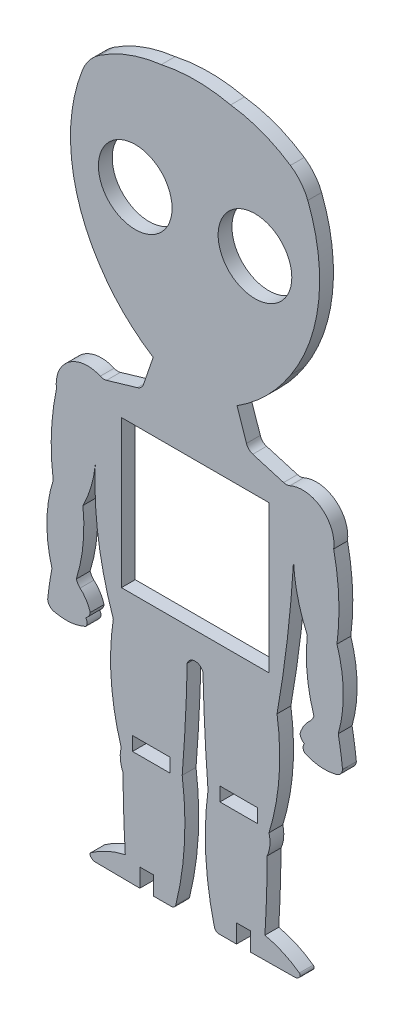
SolidWorks part; units mm, degrees
ref_plane "Alzado" through (0, 0, 0) normal (0, 0, 1) x (1, 0, 0)
ref_plane "Planta" through (0, 0, 0) normal (0, 1, 0) x (1, 0, 0)
ref_plane "Vista lateral" through (0, 0, 0) normal (1, 0, 0) x (0, 0, -1)
sketch "Model" plane through (0, 0, 0) normal (0, 0, 1) x (1, 0, 0)
  line L0 (34.7592, 26.0026) -> (50.2592, 26.0026)
  line L1 (50.2592, 26.0026) -> (50.2592, -5.9974)
  line L2 (50.2592, -5.9974) -> (18.2592, -5.9974)
  line L3 (18.2592, -5.9974) -> (18.2592, 26.0026)
  line L4 (18.2592, 26.0026) -> (33.7592, 26.0026)
  line L5 (33.7592, 26.0026) -> (34.7592, 26.0026)
  line L6 (28.8594, -35.6001) -> (20.6594, -35.6001)
  line L7 (20.6594, -35.6001) -> (20.6594, -32.6001)
  line L8 (20.6594, -32.6001) -> (28.8594, -32.6001)
  line L9 (28.8594, -32.6001) -> (28.8594, -35.6001)
  line L10 (39.6594, -35.6001) -> (39.6594, -32.6001)
  line L11 (39.6594, -32.6001) -> (47.8594, -32.6001)
  line L12 (47.8594, -32.6001) -> (47.8594, -35.6001)
  line L13 (47.8594, -35.6001) -> (39.6594, -35.6001)
  line L14 (53.4814, 31.3825) -> (46.78, 33.3535)
  line L15 (45.4231, 34.7163) -> (43.3572, 40.7676)
  line L16 (25.1545, 40.7663) -> (23.0894, 34.7147)
  line L17 (21.7328, 33.3517) -> (15.0316, 31.3797)
  line L18 (12.6958, -60.4428) -> (22.2592, -60.5334)
  line L19 (22.2592, -60.5334) -> (22.2592, -56.5317)
  line L20 (22.2592, -56.5317) -> (25.2592, -56.5317)
  line L21 (25.2592, -56.5317) -> (25.2592, -60.533)
  line L22 (25.2592, -60.533) -> (29.0981, -60.5325)
  line L23 (39.4278, -60.5317) -> (43.2592, -60.5317)
  line L24 (43.2592, -60.5317) -> (43.2592, -56.5317)
  line L25 (43.2592, -56.5317) -> (46.2592, -56.5317)
  line L26 (46.2592, -56.5317) -> (46.2592, -60.5317)
  line L27 (46.2592, -60.5317) -> (55.8301, -60.4397)
  circle A1 centre (21.2592, 70.8466) radius 8
  circle A2 centre (47.2592, 70.8466) radius 8
  arc A3 (59.2329, -10.5747) -> (57.035, -14.061) centre (64.1887, -16.135) ccw
  arc A4 (57.035, -14.061) -> (58.0202, -15.5011) centre (58.9676, -13.7958) ccw
  arc A5 (58.0202, -15.5011) -> (58.0202, -17.1684) centre (58.9771, -16.3347) ccw
  arc A6 (58.0202, -17.1684) -> (64.614, -17.8505) centre (62.2945, -8.0616) ccw
  arc A7 (64.614, -17.8505) -> (66.2814, -16.1832) centre (64.4624, -16.0316) ccw
  arc A8 (66.2814, -16.1832) -> (65.3476, -9.929) centre (-14.6011, -25.0619) ccw
  arc A9 (65.3476, -9.929) -> (65.0712, 6.7869) centre (37.3905, -2.031) ccw
  arc A10 (65.0712, 6.7869) -> (64.3565, 24.3301) centre (13.7312, 13.4815) ccw
  arc A11 (64.3565, 24.3301) -> (54.8543, 31.4719) centre (57.6075, 25.2427) ccw
  arc A12 (53.4814, 31.3825) -> (54.8543, 31.4719) centre (54.0458, 33.3012) ccw
  arc A13 (45.4231, 34.7163) -> (46.78, 33.3535) centre (47.3443, 35.2722) ccw
  arc A14 (43.3572, 40.7676) -> (55.0302, 52.4124) centre (22.6262, 73.2219) ccw
  arc A15 (55.0302, 52.4124) -> (58.7309, 87.0649) centre (23.3595, 73.3185) ccw
  arc A16 (58.7309, 87.0649) -> (54.961, 91.7604) centre (49.4101, 83.4426) ccw
  arc A17 (54.961, 91.7604) -> (41.9834, 96.649) centre (38.2562, 67.0841) ccw
  arc A18 (41.9834, 96.649) -> (26.9226, 96.6986) centre (34.3412, 62.7637) ccw
  arc A19 (26.9226, 96.6986) -> (13.5433, 91.7574) centre (30.5591, 66.268) ccw
  arc A20 (13.5433, 91.7574) -> (9.7741, 87.0613) centre (19.0954, 83.4403) ccw
  arc A21 (9.7741, 87.0613) -> (13.4798, 52.4094) centre (45.1475, 73.3201) ccw
  arc A22 (13.4798, 52.4094) -> (25.1545, 40.7663) centre (45.8808, 73.2236) ccw
  arc A23 (21.7328, 33.3517) -> (23.0894, 34.7147) centre (21.1682, 35.2703) ccw
  arc A24 (13.6588, 31.4689) -> (15.0316, 31.3797) centre (14.467, 33.2983) ccw
  arc A25 (13.6588, 31.4689) -> (4.1576, 24.3258) centre (10.9065, 25.2394) ccw
  arc A26 (4.1576, 24.3258) -> (3.4454, 6.7825) centre (54.7845, 13.4845) ccw
  arc A27 (3.4454, 6.7825) -> (3.1714, -9.9335) centre (31.1273, -2.0314) ccw
  arc A28 (3.1714, -9.9335) -> (2.2386, -16.1878) centre (83.1223, -25.0548) ccw
  arc A29 (2.2386, -16.1878) -> (3.9062, -17.8549) centre (4.0575, -16.0359) ccw
  arc A30 (3.9062, -17.8549) -> (10.4998, -17.1719) centre (6.2243, -8.0656) ccw
  arc A31 (10.4998, -17.1719) -> (10.4996, -15.5045) centre (9.5429, -16.3383) ccw
  arc A32 (10.4996, -15.5045) -> (11.4847, -14.0643) centre (9.552, -13.7993) ccw
  arc A33 (11.4847, -14.0643) -> (9.2862, -10.5783) centre (4.3312, -16.1393) ccw
  arc A34 (8.4524, -9.29) -> (9.2862, -10.5783) centre (12.0901, -7.8495) ccw
  arc A35 (8.4524, -9.29) -> (9.8956, 5.2623) centre (-25.3489, 1.41) ccw
  arc A36 (9.8956, 5.2623) -> (12.5842, 14.288) centre (-12.4585, 16.8346) ccw
  arc A37 (12.5842, 14.288) -> (16.4975, -12.7845) centre (85.553, 11.0165) ccw
  arc A38 (16.4975, -12.7845) -> (18.2118, -36.0703) centre (68.3395, -20.6738) ccw
  arc A39 (18.2118, -36.0703) -> (18.6126, -40.6193) centre (24.9113, -37.7723) ccw
  arc A40 (18.6126, -40.6193) -> (19.1045, -55.7883) centre (279.7037, -39.745) ccw
  arc A41 (19.1045, -55.7883) -> (11.6342, -59.1555) centre (23.7692, -76.1072) ccw
  arc A42 (11.6342, -59.1555) -> (11.514, -59.834) centre (11.9309, -59.558) ccw
  arc A43 (11.514, -59.834) -> (12.6958, -60.4428) centre (12.6489, -59.0825) ccw
  arc A44 (29.0981, -60.5325) -> (30.0667, -59.7805) centre (29.098, -59.5325) ccw
  arc A45 (30.0667, -59.7805) -> (31.4617, -34.7001) centre (-35.1582, -43.5737) ccw
  arc A46 (31.4617, -34.7001) -> (32.5525, -13.0644) centre (-344.2864, -4.9097) ccw
  arc A47 (35.9661, -13.0294) -> (32.5525, -13.0644) centre (34.2652, -13.622) ccw
  arc A48 (35.9661, -13.0294) -> (37.0609, -34.6995) centre (442.2785, -3.3647) ccw
  arc A49 (37.0609, -34.6995) -> (38.4591, -59.7799) centre (103.6824, -43.5646) ccw
  arc A50 (38.4591, -59.7799) -> (39.4278, -60.5317) centre (39.4278, -59.5317) ccw
  arc A51 (55.8301, -60.4397) -> (57.0118, -59.8307) centre (55.8768, -59.0794) ccw
  arc A52 (57.0118, -59.8307) -> (56.8915, -59.1522) centre (56.5949, -59.5547) ccw
  arc A53 (56.8915, -59.1522) -> (49.4209, -55.7886) centre (45.3431, -74.8232) ccw
  arc A54 (49.4209, -55.7886) -> (49.9108, -40.6171) centre (-211.2211, -39.7784) ccw
  arc A55 (49.9108, -40.6171) -> (50.311, -36.068) centre (43.6116, -37.7709) ccw
  arc A56 (50.311, -36.068) -> (52.0514, -12.8442) centre (0.3323, -20.6454) ccw
  arc A57 (52.0514, -12.8442) -> (55.6356, 17.6165) centre (-205.9662, 32.9566) ccw
  arc A58 (55.6356, 17.6165) -> (58.6212, 5.2658) centre (89.557, 19.2805) ccw
  arc A59 (58.6212, 5.2658) -> (60.0666, -9.2863) centre (93.8663, 1.4186) ccw
  arc A60 (59.2329, -10.5747) -> (60.0666, -9.2863) centre (56.4286, -7.8463) ccw
extrude "Saliente-Extruir1" add sketch "Model" along normal blind 3
